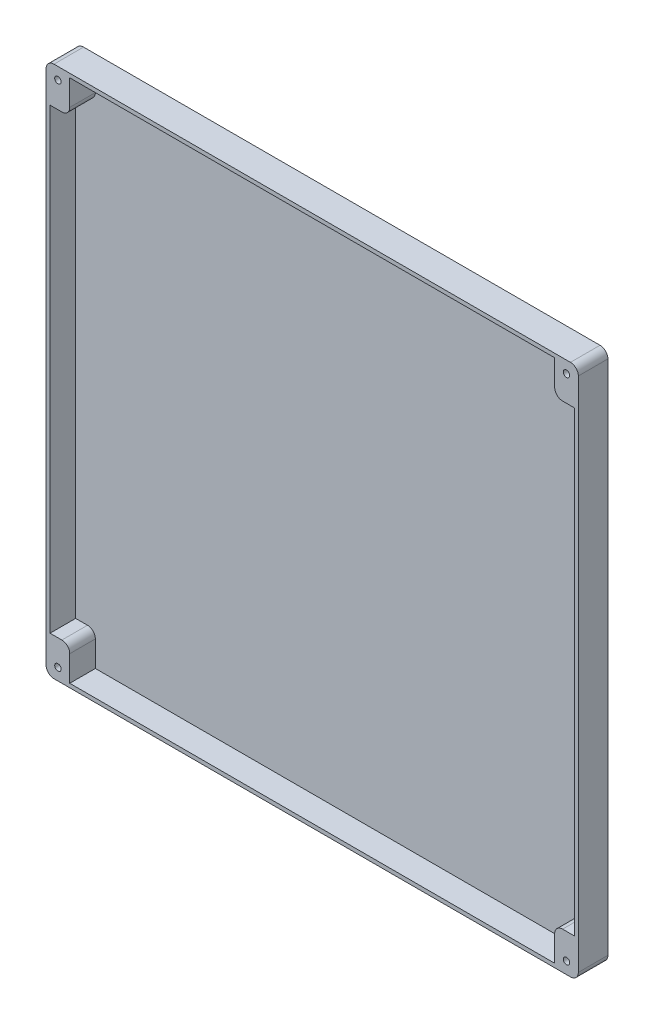
SolidWorks part; units mm, degrees
ref_plane "Plan de face" through (0, 0, 0) normal (0, 0, 1) x (1, 0, 0)
ref_plane "Plan de dessus" through (0, 0, 0) normal (0, 1, 0) x (1, 0, 0)
ref_plane "Plan de droite" through (0, 0, 0) normal (1, 0, 0) x (0, 0, -1)
sketch "Esquisse1" plane through (0, 0, 0) normal (0, 0, 1) x (1, 0, 0)
  line L1 (0, 0) -> (270, 0)
  line L2 (0, 0) -> (0, -270)
  line L3 (0, -270) -> (270, -270)
  line L4 (270, 0) -> (270, -270)
  dimension "D1" = 270
  dimension "D2" = 270
extrude "Extrusion1" add sketch "Esquisse1" along normal blind 15
fillet "Congé2" radius 4 4 edges at (0, -270, 7.5) (270, -270, 7.5) (0, 0, 7.5) (270, 0, 7.5)
sketch "Esquisse2" plane through (0, 0, 15) normal (0, 0, 1) x (1, 0, 0)
  line L0 (12, -2) -> (12, -19)
  line L1 (12, -19) -> (2, -19)
  line L2 (2, -19) -> (2, -251)
  line L3 (2, -251) -> (12, -251)
  line L4 (12, -251) -> (12, -268)
  line L5 (12, -268) -> (258, -268)
  line L6 (258, -268) -> (258, -251)
  line L7 (258, -251) -> (268, -251)
  line L8 (268, -251) -> (268, -19)
  line L9 (268, -19) -> (258, -19)
  line L10 (258, -19) -> (258, -2)
  line L11 (258, -2) -> (12, -2)
  line L12 (0, -4) -> (0, -266) construction
  line L13 (4, -270) -> (266, -270) construction
  line L14 (270, -266) -> (270, -4) construction
  line L16 (266, 0) -> (4, 0) construction
  dimension "D1" = 17
  dimension "D2" = 10
  dimension "D3" = 2
  dimension "D4" = 2
  dimension "D5" = 2
  dimension "D6" = 2
extrude "Extrusion2" cut sketch "Esquisse2" against normal blind 13
fillet "Congé3" radius 4 4 edges at (258, -19, 8.5) (258, -251, 8.5) (12, -19, 8.5) (12, -251, 8.5)
hole_wizard "Chambrage pour vis à tête ronde bombée #41" positions "Esquisse7" profile "Esquisse6" counterbore size "#4" standard "Ansi Pouces" end condition through all
sketch "Esquisse7" plane through (0, 0, 0) normal (0, 0, -1) x (-1, 0, 0)
  line L0 (-270, -266) -> (-270, -4) construction
  line L1 (-266, 0) -> (-4, 0) construction
  line L2 (0, -4) -> (0, -266) construction
  line L3 (-4, -270) -> (-266, -270) construction
  point P3 (-264, -6)
  point P5 (-6, -6)
  point P7 (-6, -264)
  point P9 (-264, -264)
  dimension "D1" = 6
  dimension "D2" = 6
  dimension "D3" = 6
  dimension "D4" = 6
  dimension "D5" = 6
  dimension "D6" = 6
  dimension "D7" = 6
  dimension "D8" = 6
sketch "Esquisse6" plane through (264, -6, 0) normal (1, 0, 0) x (0, 1, 0)
  line L0 (0, 0) -> (0, 15)
  line L1 (0, 15) -> (1.6319, 15)
  line L3 (1.6319, 15) -> (1.632, 4.032)
  line L4 (3.175, 4.032) -> (1.632, 4.032)
  line L5 (3.175, 4.032) -> (3.175, 0.635)
  line L6 (3.175, 0.635) -> (3.81, 0)
  line L7 (3.81, 0) -> (0, 0)
  line L8 (-3.175, 0.635) -> (-3.81, 0) construction
  line L11 (0, -6.35) -> (0, 107.95) construction
  dimension "Diamètre du perçage jusqu'au prochain" = 3.2639
  dimension "Profondeur du perçage jusqu'au prochain" = 15
  dimension "Diamètre du chambrage" = 6.35
  dimension "Profondeur du chambrage" = 4.032
  dimension "Diamètre du fraisage entrant" = 7.62
  dimension "Angle du fraisage entrant" = 90
